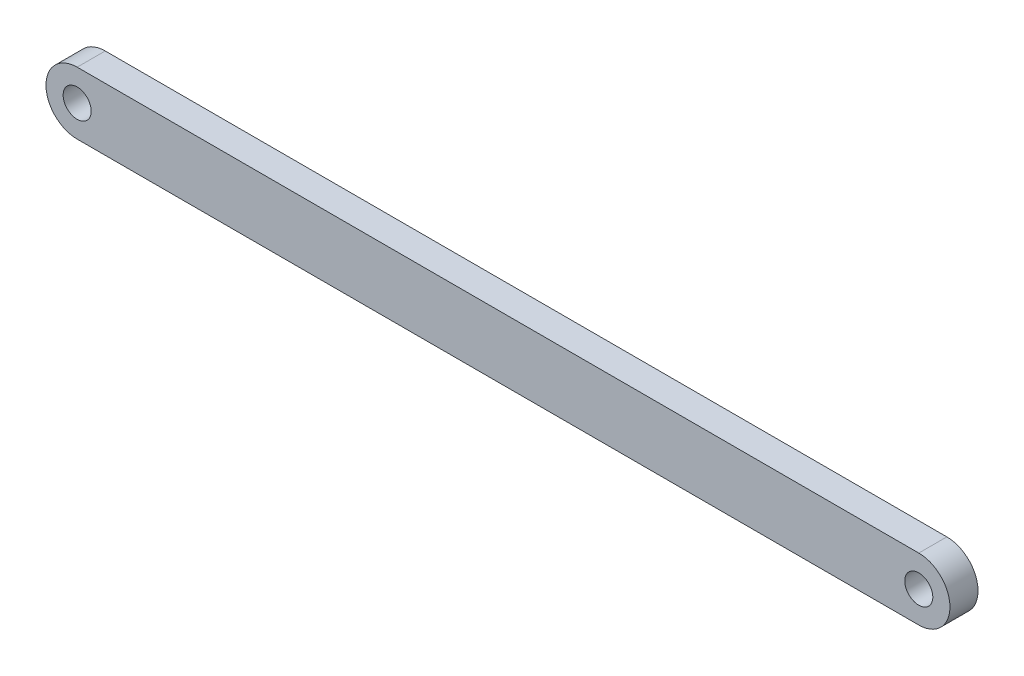
SolidWorks part; units mm, degrees
ref_plane "Płaszczyzna przednia" through (0, 0, 0) normal (0, 0, 1) x (1, 0, 0)
ref_plane "Płaszczyzna górna" through (0, 0, 0) normal (0, 1, 0) x (1, 0, 0)
ref_plane "Płaszczyzna prawa" through (0, 0, 0) normal (1, 0, 0) x (0, 0, -1)
sketch "Szkic1" plane through (0, 0, 0) normal (0, 0, 1) x (1, 0, 0)
  line L0 (0, 20) -> (540, 20)
  line L1 (0, -20) -> (540, -20)
  arc A0 (0, 20) -> (0, -20) centre (0, 0) ccw
  circle A1 centre (0, 0) radius 9
  circle A2 centre (540, 0) radius 9
  arc A3 (540, 20) -> (540, -20) centre (540, 0) cw
  dimension "D1" = 18
  dimension "D4" = 18
  dimension "D5" = 20
  dimension "D2" = 40
  dimension "D3" = 540
extrude "Dodanie-wyciągnięcie2" add sketch "Szkic1" along normal blind 18
